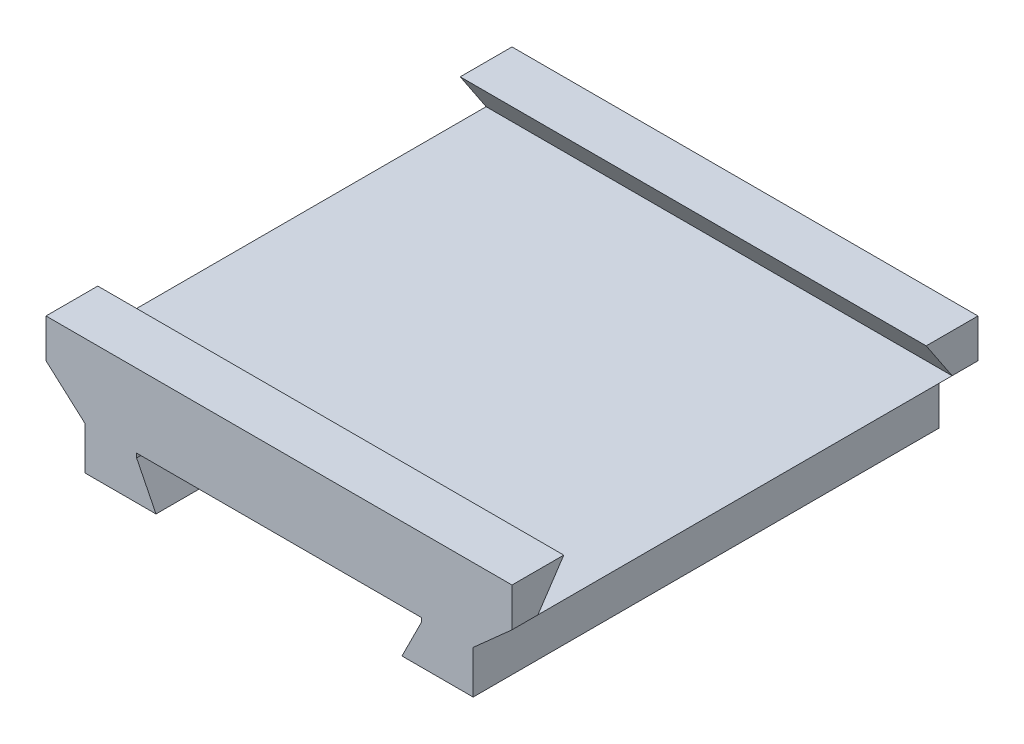
SolidWorks part; units mm, degrees
ref_plane "Front Plane" through (0, 0, 0) normal (0, 0, 1) x (1, 0, 0)
ref_plane "Top Plane" through (0, 0, 0) normal (0, 1, 0) x (1, 0, 0)
ref_plane "Right Plane" through (0, 0, 0) normal (1, 0, 0) x (0, 0, -1)
sketch "Sketch1" plane through (0, 0, 0) normal (0, 0, 1) x (1, 0, 0)
  line L1 (-55, -61) -> (-47.5, -76)
  line L3 (-47.5, -76) -> (-75, -76)
  line L5 (47.5, -76) -> (55, -61)
  line L7 (75, -76) -> (47.5, -76)
  line L8 (-75, -76) -> (-75, -59.3738)
  line L9 (-75, -59.3738) -> (-90, -46)
  line L10 (-90, -46) -> (-90, -31)
  line L11 (-90, -31) -> (90, -31)
  line L12 (90, -31) -> (90, -46)
  line L13 (90, -46) -> (75, -59.3738)
  line L14 (75, -59.3738) -> (75, -76)
  line L15 (-55, -61) -> (-55, -59.3738)
  line L16 (-55, -59.3738) -> (55, -59.3738)
  line L17 (55, -59.3738) -> (55, -61)
  line L18 (0, 0) -> (0, -177.1991) construction
  line L19 (-162.5771, 0) -> (118.8501, 0) construction
  point P19 (0, -31)
  dimension "D1" = 180
  dimension "D2" = 45
  dimension "D3" = 15
extrude "Boss-Extrude1" add sketch "Sketch1" along normal mid plane 180
sketch "Sketch2" plane through (90, 0, 0) normal (1, 0, 0) x (0, 0, -1)
  line L0 (0, 45.5955) -> (0, -178.4043) construction
  line L1 (-98.6829, 0) -> (102.0975, 0) construction
  line L2 (-70, -31) -> (-80, -46)
  line L3 (-90, -31) -> (90, -31) construction
  line L4 (-90, -46) -> (90, -46) construction
  line L5 (-80, -46) -> (80, -46)
  line L6 (80, -46) -> (70, -31)
  line L7 (70, -31) -> (-70, -31)
  line L8 (-90, -46) -> (-90, -31) construction
  point P13 (0, -46)
  point P14 (0, -31)
  dimension "D1" = 20
  dimension "D2" = 10
extrude "Cut-Extrude1" cut sketch "Sketch2" against normal blind 180
